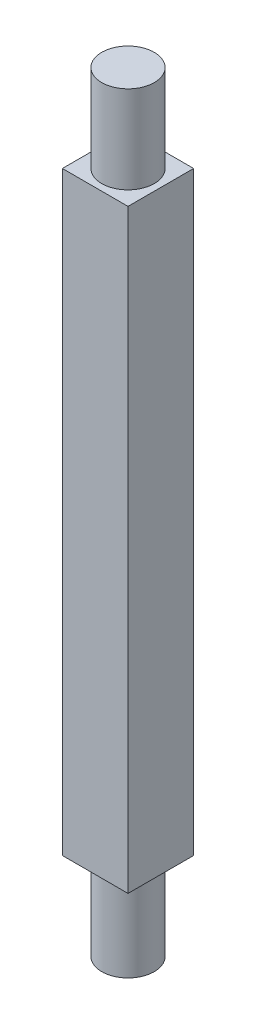
SolidWorks part; units mm, degrees
ref_plane "前视基准面" through (0, 0, 0) normal (0, 0, 1) x (1, 0, 0)
ref_plane "上视基准面" through (0, 0, 0) normal (0, 1, 0) x (1, 0, 0)
ref_plane "右视基准面" through (0, 0, 0) normal (1, 0, 0) x (0, 0, -1)
other "Configuration Table"
sketch "草图1" plane through (0, 0, 0) normal (0, 1, 0) x (1, 0, 0)
  line L1 (7.5, -7.5) -> (-7.5, -7.5)
  line L2 (7.5, -7.5) -> (7.5, 7.5)
  line L3 (7.5, 7.5) -> (-7.5, 7.5)
  line L4 (-7.5, -7.5) -> (-7.5, 7.5)
  line L5 (7.5, -7.5) -> (-7.5, 7.5) construction
  line L6 (7.5, 7.5) -> (-7.5, -7.5) construction
  point P0 (0, 0)
  dimension "D1" = 15
  dimension "D2" = 15
extrude "凸台-拉伸1" add sketch "草图1" along normal blind 136 contours L4 L3 L2 L1
sketch "草图2" plane through (0, 136, 0) normal (0, 1, 0) x (1, 0, 0)
  circle A0 centre (0, 0) radius 6
  dimension "D1" = 12
extrude "凸台-拉伸2" add sketch "草图2" along normal blind 20 contours A0
sketch "草图3" plane through (0, 0, 0) normal (0, -1, 0) x (1, 0, 0)
  circle A0 centre (0, 0) radius 6
  dimension "D1" = 12
extrude "凸台-拉伸3" add sketch "草图3" along normal blind 20 contours A0
